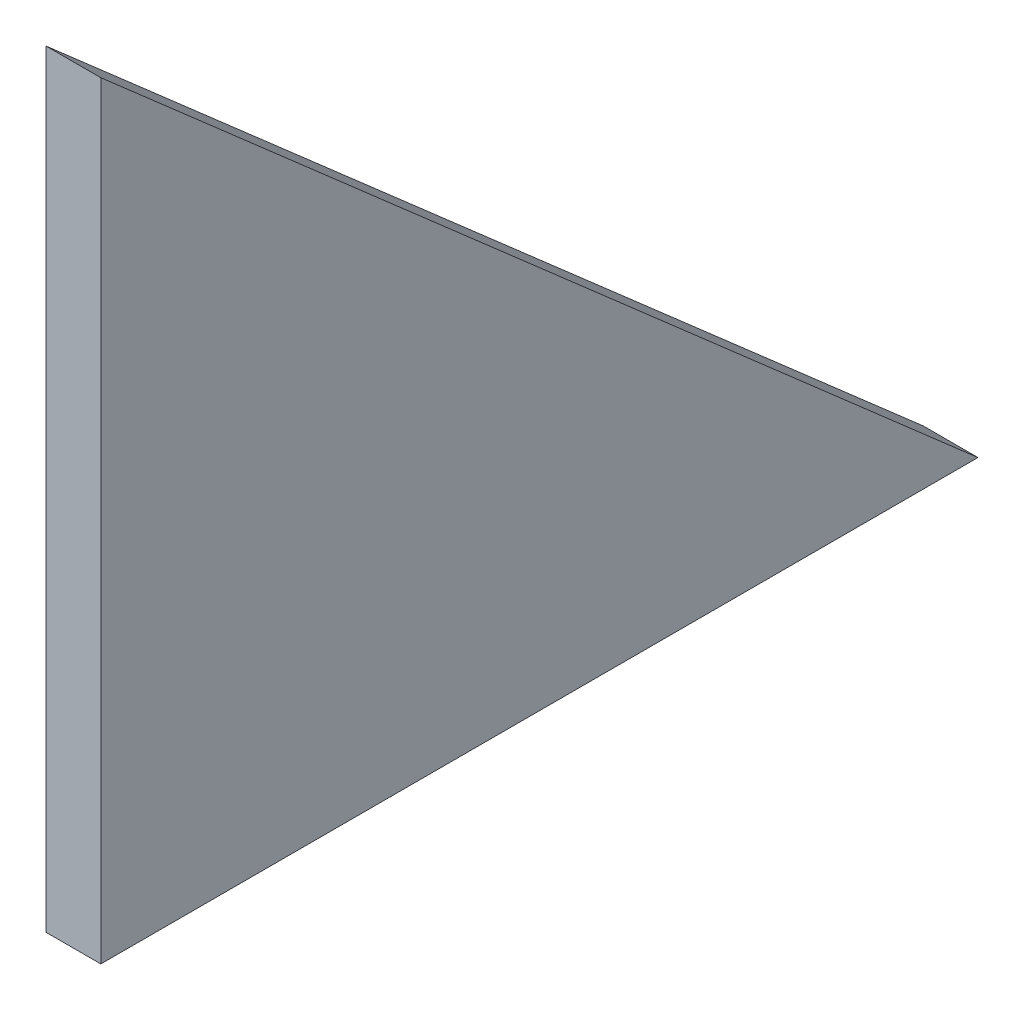
SolidWorks part; units mm, degrees
ref_plane "Front Plane" through (0, 0, 0) normal (0, 0, 1) x (1, 0, 0)
ref_plane "Top Plane" through (0, 0, 0) normal (0, 1, 0) x (1, 0, 0)
ref_plane "Right Plane" through (0, 0, 0) normal (1, 0, 0) x (0, 0, -1)
sketch "Sketch1" plane through (0, 0, 0) normal (1, 0, 0) x (0, 0, -1)
  line L2 (0, 0) -> (0, 70)
  line L3 (0, 70) -> (80, 0)
  line L4 (80, 0) -> (0, 0)
  dimension "D3" = 70
  dimension "D4" = 80
extrude "Boss-Extrude1" add sketch "Sketch1" along normal blind 5
